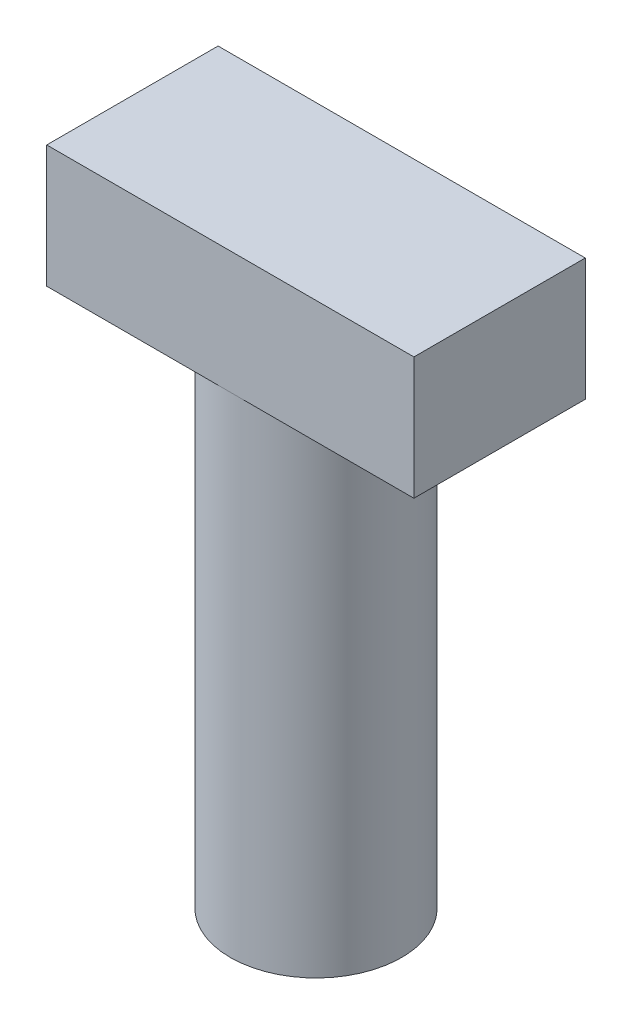
SolidWorks part; units mm, degrees
ref_plane "Front Plane" through (0, 0, 0) normal (0, 0, 1) x (1, 0, 0)
ref_plane "Top Plane" through (0, 0, 0) normal (0, 1, 0) x (1, 0, 0)
ref_plane "Right Plane" through (0, 0, 0) normal (1, 0, 0) x (0, 0, -1)
sketch "Sketch2" plane through (0, 0, 0) normal (0, 1, 0) x (1, 0, 0)
  line L1 (-15, 7) -> (15, 7)
  line L2 (-15, 7) -> (-15, -7)
  line L3 (-15, -7) -> (15, -7)
  line L4 (15, 7) -> (15, -7)
  dimension "D1" = 14
  dimension "D2" = 30
  dimension "D3" = 7
  dimension "D4" = 15
extrude "Boss-Extrude1" add sketch "Sketch2" against normal blind 10
sketch "Sketch3" plane through (0, -10, 0) normal (0, -1, 0) x (1, 0, 0)
  circle A0 centre (0, 0) radius 7
  dimension "D1" = 14
extrude "Boss-Extrude2" add sketch "Sketch3" along normal blind 40
